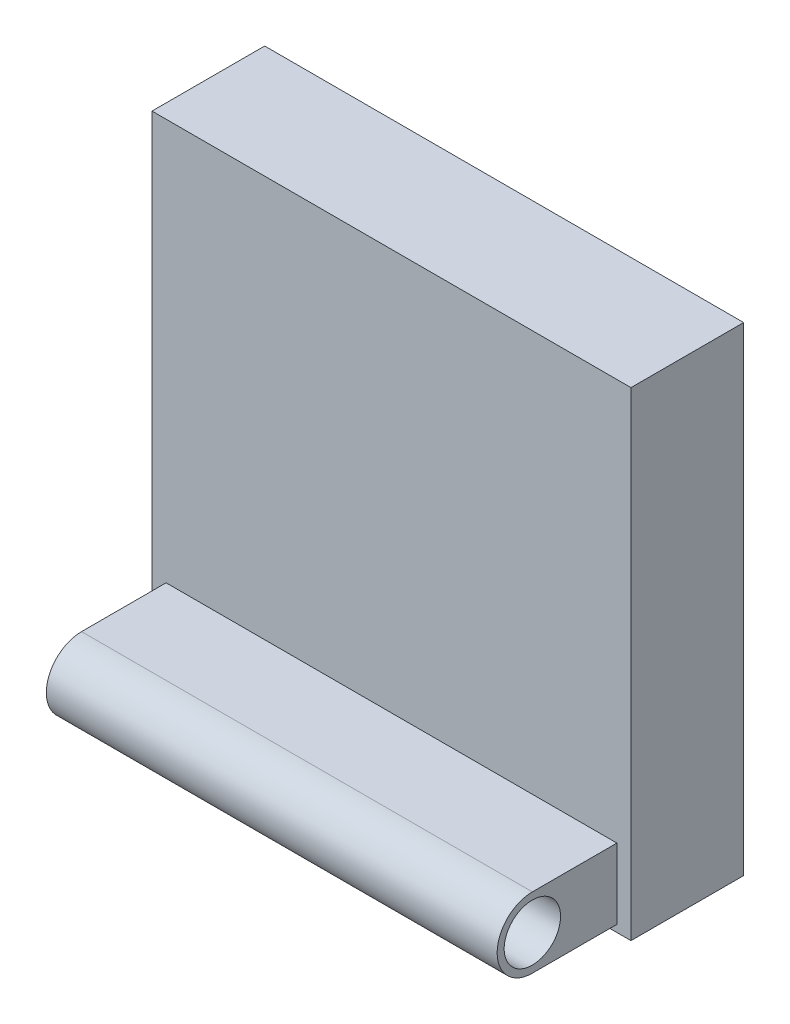
SolidWorks part; units mm, degrees
ref_plane "Plan de face" through (0, 0, 0) normal (0, 0, 1) x (1, 0, 0)
ref_plane "Plan de dessus" through (0, 0, 0) normal (0, 1, 0) x (1, 0, 0)
ref_plane "Plan de droite" through (0, 0, 0) normal (1, 0, 0) x (0, 0, -1)
sketch "Esquisse1" plane through (0, 0, 0) normal (0, 0, 1) x (1, 0, 0)
  line L1 (0, 0) -> (34, 0)
  line L2 (0, 0) -> (0, 34)
  line L3 (0, 34) -> (34, 34)
  line L4 (34, 0) -> (34, 34)
  dimension "D1" = 34
  dimension "D2" = 34
extrude "Boss.-Extru.1" add sketch "Esquisse1" along normal blind 8 contours L2 L1 L4 L3
sketch "Esquisse2" plane through (0, 0, 0) normal (1, 0, 0) x (0, 0, -1)
  line L0 (-8, 0) -> (-8, 34) construction
  line L1 (-8, 5.5) -> (-14, 5.5)
  line L2 (-14, 0.5) -> (-8, 0.5)
  line L3 (-8, 0) -> (0, 0) construction
  line L4 (-8, 5.5) -> (-8, 0.5)
  arc A0 (-14, 5.5) -> (-14, 0.5) centre (-14, 3) ccw
  circle A1 centre (-14, 3) radius 2
  dimension "D1" = 5
  dimension "D4" = 4
  dimension "D2" = 6
  dimension "D3" = 3
extrude "Boss.-Extru.2" add sketch "Esquisse2" along normal blind 32 from offset 1
